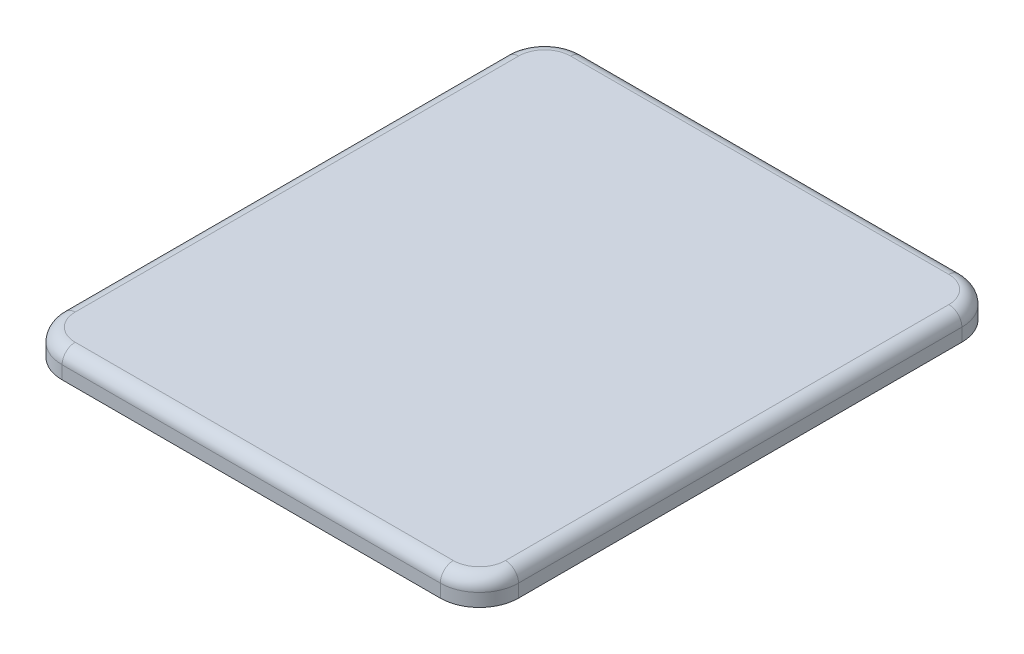
SolidWorks part; units mm, degrees
material "Polyurethane Foam Flexible"
ref_plane "Front Plane" through (0, 0, 0) normal (0, 0, 1) x (1, 0, 0)
ref_plane "Top Plane" through (0, 0, 0) normal (0, 1, 0) x (1, 0, 0)
ref_plane "Right Plane" through (0, 0, 0) normal (1, 0, 0) x (0, 0, -1)
sketch "Sketch1" plane through (0, 0, 0) normal (0, 1, 0) x (1, 0, 0)
  line L1 (-145, -200) -> (145, -200)
  line L2 (-175, -170) -> (-175, 170)
  line L3 (-145, 200) -> (145, 200)
  line L4 (175, -170) -> (175, 170)
  line L5 (-175, -200) -> (175, 200) construction
  line L6 (-175, 200) -> (175, -200) construction
  arc A0 (-175, -170) -> (-145, -200) centre (-145, -170) ccw
  arc A1 (145, -200) -> (175, -170) centre (145, -170) ccw
  arc A2 (175, 170) -> (145, 200) centre (145, 170) ccw
  arc A3 (-145, 200) -> (-175, 170) centre (-145, 170) ccw
  point P0 (0, 0)
  dimension "D3" = 30
  dimension "D1" = 350
  dimension "D2" = 400
extrude "Boss-Extrude1" add sketch "Sketch1" along normal blind 20
fillet "Fillet1" radius 10 8 edges at (-175, 20, 0) (-166.2132, 20, -191.2132) (0, 20, -200) (166.2132, 20, -191.2132) (175, 20, 0) (166.2132, 20, 191.2132) (0, 20, 200) (-166.2132, 20, 191.2132)
